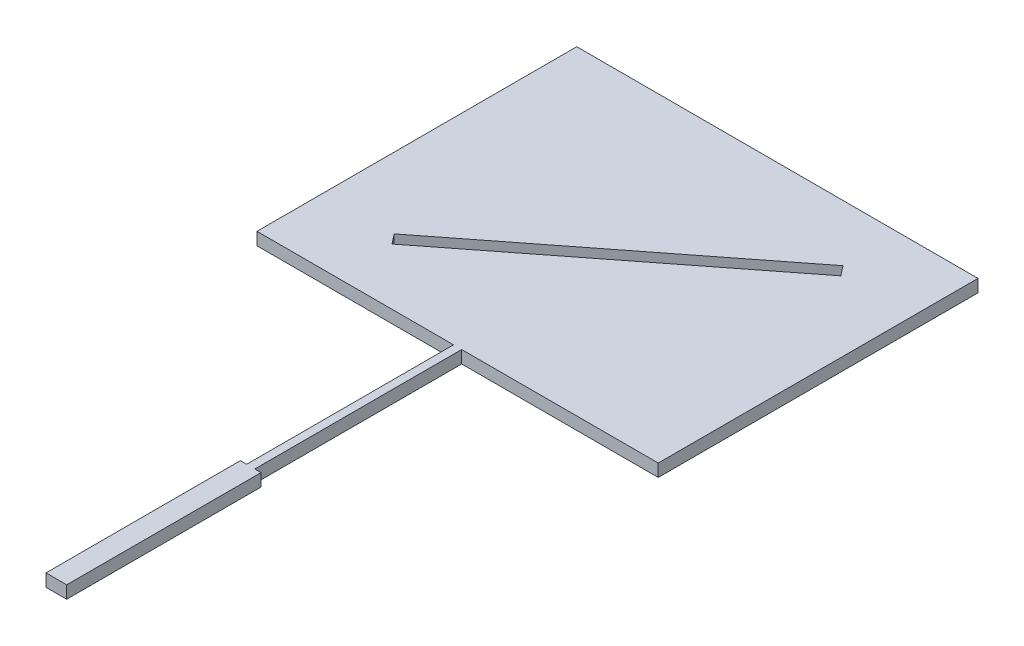
SolidWorks part; units mm, degrees
ref_plane "Front Plane" through (0, 0, 0) normal (0, 0, 1) x (1, 0, 0)
ref_plane "Top Plane" through (0, 0, 0) normal (0, 1, 0) x (1, 0, 0)
ref_plane "Right Plane" through (0, 0, 0) normal (1, 0, 0) x (0, 0, -1)
sketch "Sketch1" plane through (0, 0, 0) normal (0, 1, 0) x (1, 0, 0)
  line L0 (0, 0) -> (3.3, 0)
  line L1 (3.3, 0) -> (3.3, 31)
  line L2 (3.3, 31) -> (2.3, 31)
  line L3 (2.3, 31) -> (2.3, 64)
  line L4 (2.3, 64) -> (33.65, 64)
  line L5 (33.65, 64) -> (33.65, 115)
  line L6 (33.65, 115) -> (-30.35, 115)
  line L7 (-30.35, 115) -> (-30.35, 64)
  line L8 (-30.35, 64) -> (1, 64)
  line L9 (1, 64) -> (1, 31)
  line L10 (1, 31) -> (0, 31)
  line L11 (0, 31) -> (0, 0)
  point P3 (3.3, 31)
  point P14 (1, 45.8707)
  point P15 (2.3, 31)
  point P16 (2.3, 45.0719)
  dimension "D1" = 3.3
  dimension "D2" = 1.3
  dimension "D3" = 31
  dimension "D4" = 64
  dimension "D5" = 51
  dimension "D6" = 33
extrude "Boss-Extrude1" add sketch "Sketch1" along normal blind 2
sketch "Sketch2" plane through (0, 2, 0) normal (0, 1, 0) x (1, 0, 0)
  line L0 (1.65, 115) -> (1.65, 64) construction
  line L1 (33.65, 115) -> (-30.35, 115) construction
  line L2 (1.65, 89.5) -> (21.7443, 105.1994) construction
  line L3 (-30.35, 64) -> (1, 64) construction
  line L4 (1.65, 89.5) -> (33.65, 89.5) construction
  line L5 (33.65, 64) -> (33.65, 115) construction
  line L6 (21.7443, 105.1994) -> (22.3599, 104.4114)
  line L7 (22.3599, 104.4114) -> (-17.8286, 73.0126)
  line L8 (-17.8286, 73.0126) -> (-19.0599, 74.5886)
  line L9 (-19.0599, 74.5886) -> (21.1286, 105.9874)
  line L10 (21.1286, 105.9874) -> (21.7443, 105.1994)
  dimension "D1" = 25.5
  dimension "D2" = 38
  dimension "D3" = 1
  dimension "D4" = 51
extrude "Cut-Extrude1" cut sketch "Sketch2" against normal through all
